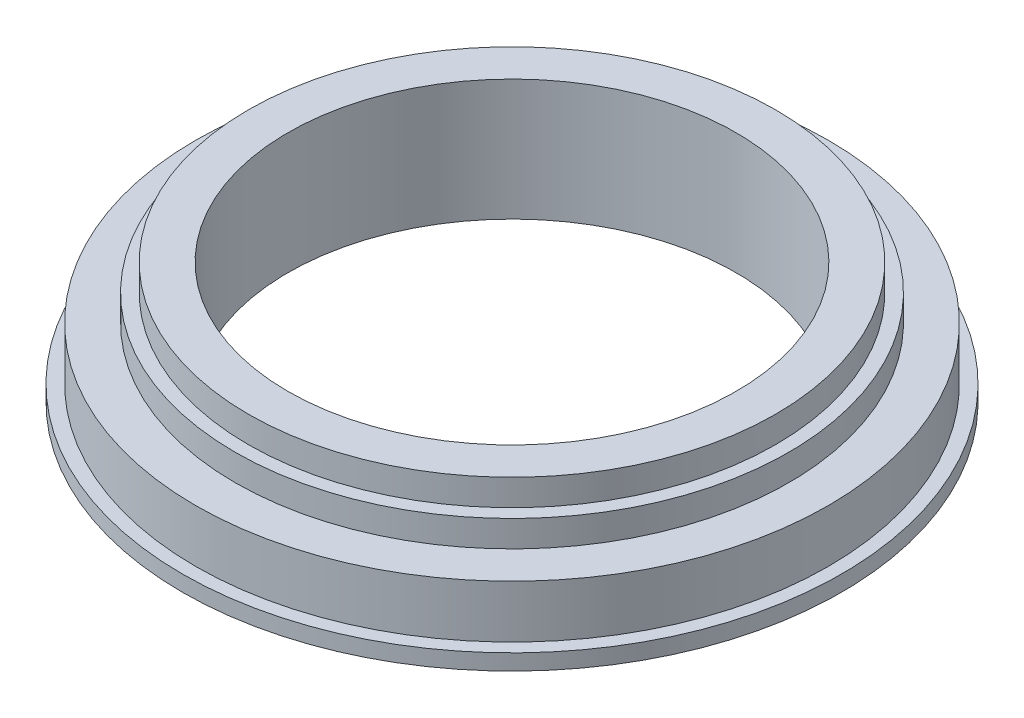
SolidWorks part; units mm, degrees
ref_plane "Front Plane" through (0, 0, 0) normal (0, 0, 1) x (1, 0, 0)
ref_plane "Top Plane" through (0, 0, 0) normal (0, 1, 0) x (1, 0, 0)
ref_plane "Right Plane" through (0, 0, 0) normal (1, 0, 0) x (0, 0, -1)
sketch "Sketch1" plane through (0, 0, 0) normal (0, 1, 0) x (1, 0, 0)
  circle A0 centre (0, 0) radius 62.5
  dimension "D1" = 125
extrude "Boss-Extrude1" add sketch "Sketch1" along normal blind 3
sketch "Sketch2" plane through (0, 3, 0) normal (0, 1, 0) x (1, 0, 0)
  circle A0 centre (0, 0) radius 60
  circle A1 centre (0, 0) radius 52.5
  dimension "D1" = 120
  dimension "D2" = 105
extrude "Boss-Extrude2" add sketch "Sketch2" along normal blind 10
sketch "Sketch3" plane through (0, 3, 0) normal (0, 1, 0) x (1, 0, 0)
  circle A0 centre (0, 0) radius 52.5
  circle A1 centre (0, 0) radius 50
  dimension "D1" = 100
extrude "Boss-Extrude3" add sketch "Sketch3" along normal blind 15
sketch "Sketch4" plane through (0, 3, 0) normal (0, 1, 0) x (1, 0, 0)
  circle A0 centre (0, 0) radius 50
  circle A1 centre (0, 0) radius 42.5
  dimension "D1" = 85
extrude "Boss-Extrude4" add sketch "Sketch4" along normal blind 20
sketch "Sketch5" plane through (0, 3, 0) normal (0, 1, 0) x (1, 0, 0)
  circle A0 centre (0, 0) radius 42.5
extrude "Cut-Extrude1" cut sketch "Sketch5" against normal through all
